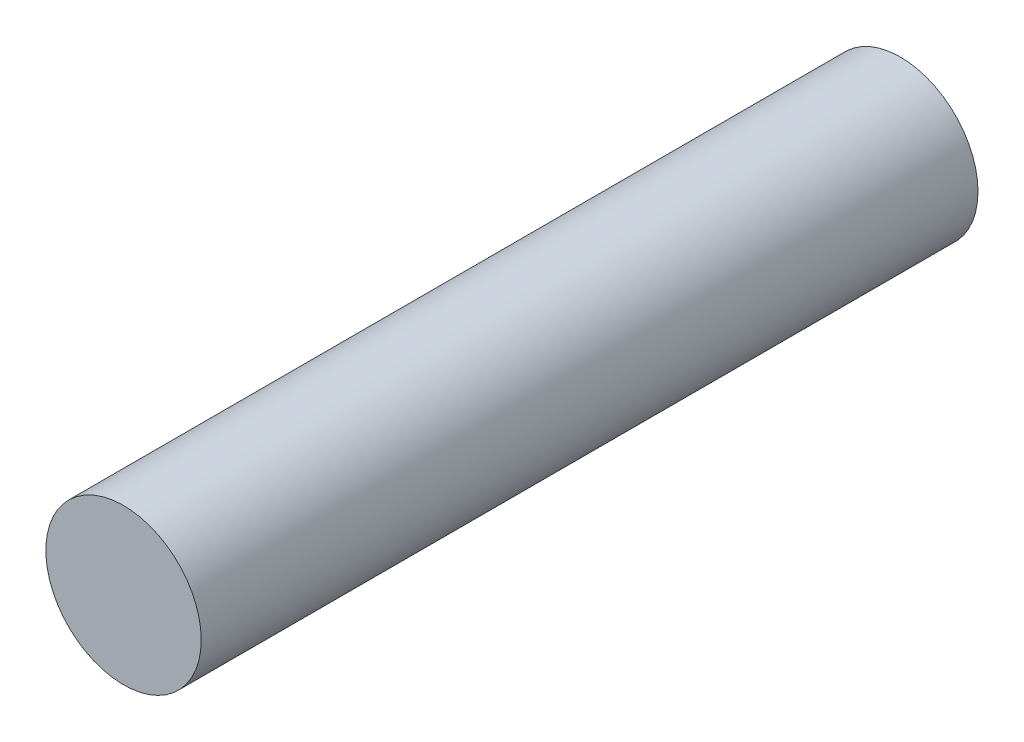
SolidWorks part; units mm, degrees
ref_plane "Front Plane" through (0, 0, 0) normal (0, 0, 1) x (1, 0, 0)
ref_plane "Top Plane" through (0, 0, 0) normal (0, 1, 0) x (1, 0, 0)
ref_plane "Right Plane" through (0, 0, 0) normal (1, 0, 0) x (0, 0, -1)
sketch "Sketch1" plane through (0, 0, 0) normal (0, 0, 1) x (1, 0, 0)
  circle A0 centre (0, 0) radius 10
  dimension "D1" = 20
extrude "Boss-Extrude1" add sketch "Sketch1" along normal blind 100
